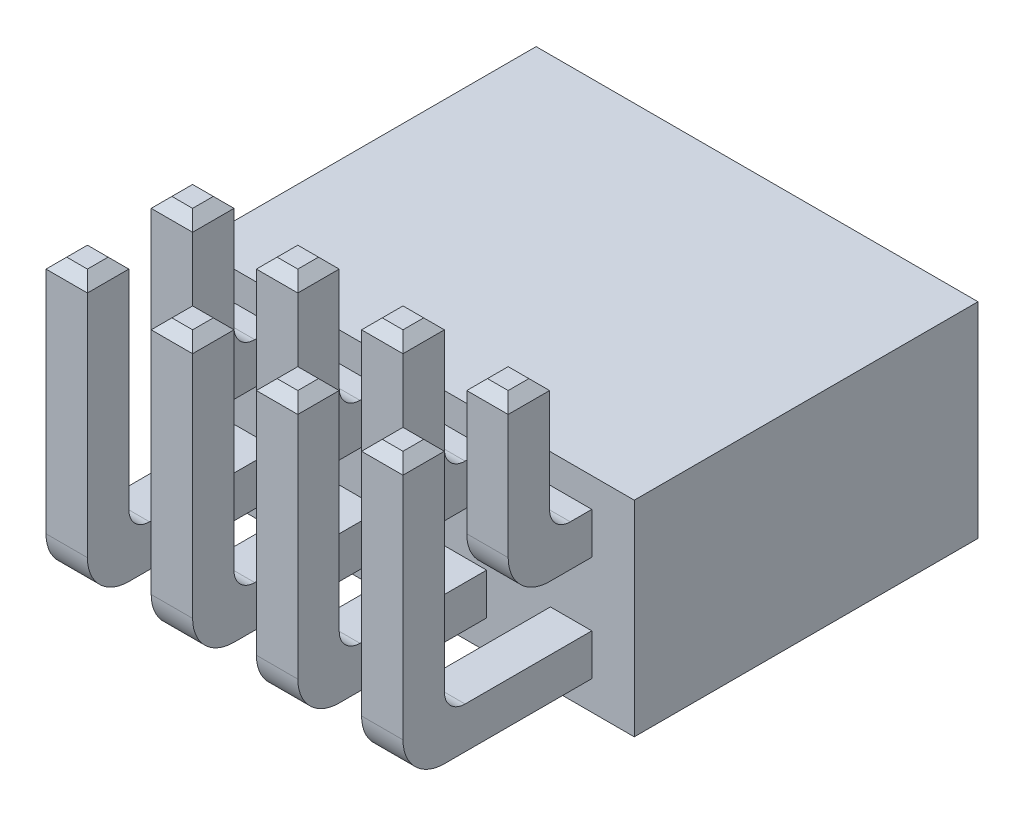
SolidWorks part; units mm, degrees
ref_plane "Front Plane" through (0, 0, 0) normal (0, 0, 1) x (1, 0, 0)
ref_plane "Top Plane" through (0, 0, 0) normal (0, 1, 0) x (1, 0, 0)
ref_plane "Right Plane" through (0, 0, 0) normal (1, 0, 0) x (0, 0, -1)
sketch "Sketch1" plane through (0, 0, 0) normal (0, 0, 1) x (1, 0, 0)
  line L1 (-5.335, 2.475) -> (5.335, 2.475)
  line L2 (-5.335, 2.475) -> (-5.335, -2.475)
  line L3 (-5.335, -2.475) -> (5.335, -2.475)
  line L4 (5.335, 2.475) -> (5.335, -2.475)
  line L5 (-5.335, 2.475) -> (5.335, -2.475) construction
  line L6 (-5.335, -2.475) -> (5.335, 2.475) construction
  point P0 (0, 0)
  dimension "D1" = 10.67
  dimension "D2" = 4.95
extrude "Boss-Extrude1" add sketch "Sketch1" along normal blind 8.3
sketch "Sketch3" plane through (0, 0, 0) normal (0, 0, -1) x (-1, 0, 0)
  line L0 (-0.5788, 0.5788) -> (-1.9612, 0.5788)
  line L5 (-3.1188, 0.5788) -> (-4.5012, 0.5788)
  line L6 (-3.1188, 0.5788) -> (-3.1188, 1.9612)
  line L7 (-3.1188, 1.9612) -> (-4.5012, 1.9612)
  line L8 (-4.5012, 0.5788) -> (-4.5012, 1.9612)
  line L9 (-3.1188, 0.5788) -> (-4.5012, 1.9612) construction
  line L10 (-3.1188, 1.9612) -> (-4.5012, 0.5788) construction
  line L11 (-0.5788, 0.5788) -> (-0.5788, 1.9612)
  line L12 (-0.5788, 1.9612) -> (-1.9612, 1.9612)
  line L13 (-1.9612, 0.5788) -> (-1.9612, 1.9612)
  line L14 (-0.5788, 0.5788) -> (-1.9612, 1.9612) construction
  line L15 (-0.5788, 1.9612) -> (-1.9612, 0.5788) construction
  line L16 (1.9612, 0.5788) -> (0.5788, 0.5788)
  line L17 (1.9612, 0.5788) -> (1.9612, 1.9612)
  line L18 (1.9612, 1.9612) -> (0.5788, 1.9612)
  line L19 (0.5788, 0.5788) -> (0.5788, 1.9612)
  line L20 (1.9612, 0.5788) -> (0.5788, 1.9612) construction
  line L21 (1.9612, 1.9612) -> (0.5788, 0.5788) construction
  line L22 (4.5012, 0.5788) -> (3.1188, 0.5788)
  line L23 (4.5012, 0.5788) -> (4.5012, 1.9612)
  line L24 (4.5012, 1.9612) -> (3.1188, 1.9612)
  line L25 (3.1188, 0.5788) -> (3.1188, 1.9612)
  line L26 (4.5012, 0.5788) -> (3.1188, 1.9612) construction
  line L27 (4.5012, 1.9612) -> (3.1188, 0.5788) construction
  line L28 (-0.5788, -1.9612) -> (-1.9612, -1.9612)
  line L29 (-0.5788, -1.9612) -> (-0.5788, -0.5788)
  line L30 (-0.5788, -0.5788) -> (-1.9612, -0.5788)
  line L31 (-1.9612, -1.9612) -> (-1.9612, -0.5788)
  line L32 (-0.5788, -1.9612) -> (-1.9612, -0.5788) construction
  line L33 (-0.5788, -0.5788) -> (-1.9612, -1.9612) construction
  line L34 (1.9612, -1.9612) -> (0.5788, -1.9612)
  line L35 (1.9612, -1.9612) -> (1.9612, -0.5788)
  line L36 (1.9612, -0.5788) -> (0.5788, -0.5788)
  line L37 (0.5788, -1.9612) -> (0.5788, -0.5788)
  line L38 (1.9612, -1.9612) -> (0.5788, -0.5788) construction
  line L39 (1.9612, -0.5788) -> (0.5788, -1.9612) construction
  line L40 (4.5012, -1.9612) -> (3.1188, -1.9612)
  line L41 (4.5012, -1.9612) -> (4.5012, -0.5788)
  line L42 (4.5012, -0.5788) -> (3.1188, -0.5788)
  line L43 (3.1188, -1.9612) -> (3.1188, -0.5788)
  line L44 (4.5012, -1.9612) -> (3.1188, -0.5788) construction
  line L45 (4.5012, -0.5788) -> (3.1188, -1.9612) construction
  line L46 (-3.1188, -1.9612) -> (-4.5012, -1.9612)
  line L47 (-3.1188, -1.9612) -> (-3.1188, -0.5788)
  line L48 (-3.1188, -0.5788) -> (-4.5012, -0.5788)
  line L49 (-4.5012, -1.9612) -> (-4.5012, -0.5788)
  line L50 (-3.1188, -1.9612) -> (-4.5012, -0.5788) construction
  line L51 (-3.1188, -0.5788) -> (-4.5012, -1.9612) construction
  line L52 (-1.27, -1.27) -> (1.27, -1.27) construction
  line L53 (-3.81, 1.27) -> (-3.81, -1.27) construction
  point P0 (-3.81, 1.27)
  point P6 (-1.27, 1.27)
  point P12 (1.27, 1.27)
  point P17 (3.81, 1.27)
  point P22 (-1.27, -1.27)
  point P27 (1.27, -1.27)
  point P32 (3.81, -1.27)
  point P37 (-3.81, -1.27)
  point P42 (0, -1.27)
  point P46 (-3.81, 0)
  dimension "D3" = 2.54
  dimension "D4" = 2.54
  dimension "D1" = 4
  dimension "D2" = 2
extrude "Cut-Extrude1" cut sketch "Sketch3" against normal blind 3
sketch "Sketch4" plane through (0, 0, 0) normal (1, 0, 0) x (0, 0, -1)
  line L0 (-8.3, 0.77) -> (-9.32, 0.77)
  line L1 (-8.3, -2.475) -> (-8.3, 2.475) construction
  line L2 (-10.32, 1.77) -> (-10.32, 5.015)
  line L3 (-10.32, 5.015) -> (-9.32, 5.015)
  line L4 (-9.32, 5.015) -> (-9.32, 2.27)
  line L5 (-8.82, 1.77) -> (-8.3, 1.77)
  line L6 (-8.3, 1.77) -> (-8.3, 0.77)
  line L7 (-8.3, -1.77) -> (-11.86, -1.77)
  line L8 (-12.86, -0.77) -> (-12.86, 5.015)
  line L9 (-12.86, 5.015) -> (-11.86, 5.015)
  line L10 (-11.86, 5.015) -> (-11.86, -0.27)
  line L11 (-11.36, -0.77) -> (-8.3, -0.77)
  line L12 (-8.3, -0.77) -> (-8.3, -1.77)
  line L13 (-8.3, 2.475) -> (0, 2.475) construction
  line L14 (-8.3, -1.27) -> (-8.3, 1.27) construction
  arc A0 (-11.86, -0.27) -> (-11.36, -0.77) centre (-11.36, -0.27) ccw
  arc A1 (-9.32, 2.27) -> (-8.82, 1.77) centre (-8.82, 2.27) ccw
  arc A2 (-11.86, -1.77) -> (-12.86, -0.77) centre (-11.86, -0.77) cw
  arc A3 (-9.32, 0.77) -> (-10.32, 1.77) centre (-9.32, 1.77) cw
  point P10 (-9.82, 5.015)
  point P15 (-12.36, 5.015)
  point P18 (-8.3, -1.27)
  point P19 (-8.3, 1.27)
  point P22 (-8.3, 0)
  dimension "D6" = 0.5
  dimension "D7" = 1
  dimension "D1" = 2.54
  dimension "D2" = 2.54
  dimension "D3" = 1.52
  dimension "D4" = 1
  dimension "D5" = 2.54
extrude "Boss-Extrude2" add sketch "Sketch4" along normal blind 1 from offset 3.31
pattern_linear "LPattern1" count 4 spacing 2.54 along (-1, 0, 0) of "Boss-Extrude2"
chamfer "Chamfer1" distance 0.25 angle 45 32 edges at (-3.81, 5.015, 11.86) (-3.31, 5.015, 12.36) (-3.81, 5.015, 12.86) (-4.31, 5.015, 12.36) (-1.27, 5.015, 11.86) (-0.77, 5.015, 12.36) (-1.27, 5.015, 12.86) (-1.77, 5.015, 12.36) (1.27, 5.015, 11.86) (1.77, 5.015, 12.36) (1.27, 5.015, 12.86) (0.77, 5.015, 12.36) (3.81, 5.015, 11.86) (4.31, 5.015, 12.36) (3.81, 5.015, 12.86) (3.31, 5.015, 12.36) (3.81, 5.015, 9.32) (4.31, 5.015, 9.82) (3.81, 5.015, 10.32) (3.31, 5.015, 9.82) (1.27, 5.015, 9.32) (1.77, 5.015, 9.82) (1.27, 5.015, 10.32) (0.77, 5.015, 9.82) (-1.27, 5.015, 9.32) (-0.77, 5.015, 9.82) (-1.27, 5.015, 10.32) (-1.77, 5.015, 9.82) (-3.81, 5.015, 9.32) (-3.31, 5.015, 9.82) (-3.81, 5.015, 10.32) (-4.31, 5.015, 9.82)
